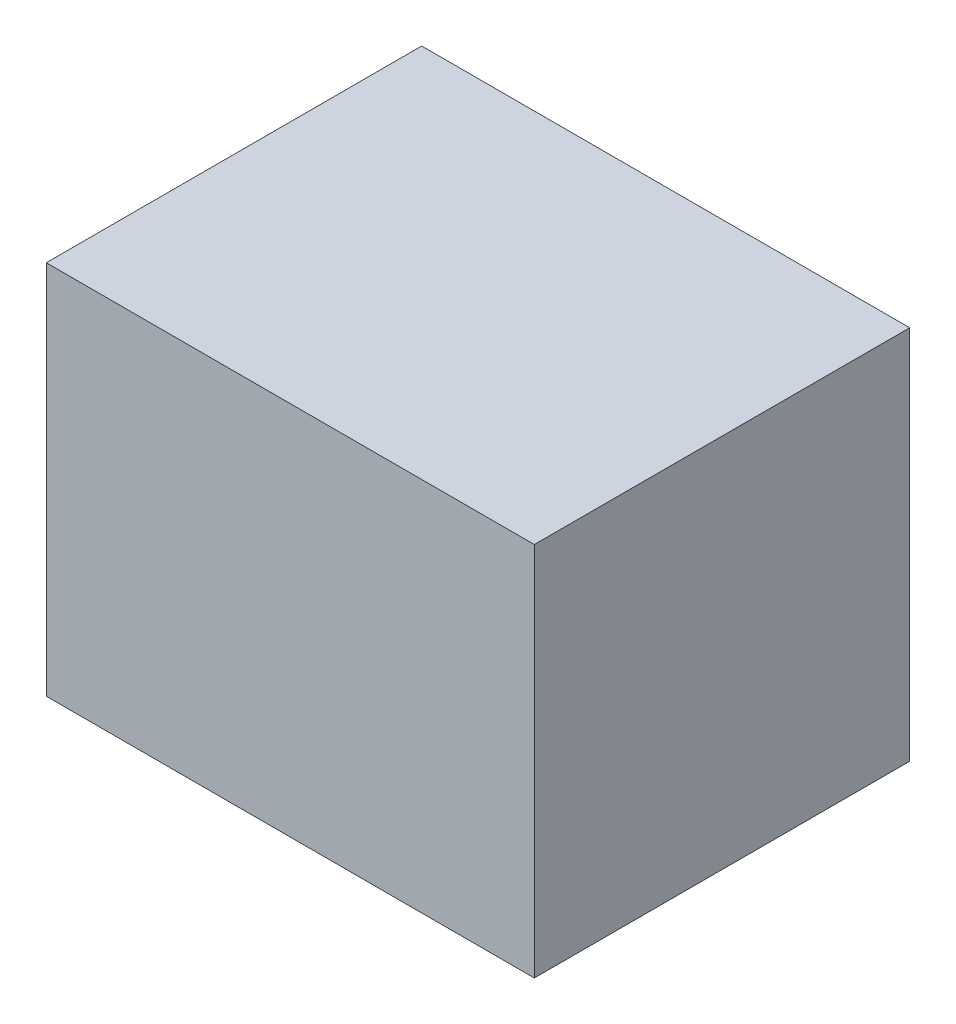
SolidWorks part; units mm, degrees
ref_plane "Front Plane" through (0, 0, 0) normal (0, 0, 1) x (1, 0, 0)
ref_plane "Top Plane" through (0, 0, 0) normal (0, 1, 0) x (1, 0, 0)
ref_plane "Right Plane" through (0, 0, 0) normal (1, 0, 0) x (0, 0, -1)
sketch "Sketch1" plane through (0, 0, 0) normal (0, 1, 0) x (1, 0, 0)
  line L1 (-325, 250) -> (325, 250)
  line L2 (-325, 250) -> (-325, -250)
  line L3 (-325, -250) -> (325, -250)
  line L4 (325, 250) -> (325, -250)
  line L5 (-325, 250) -> (325, -250) construction
  line L6 (-325, -250) -> (325, 250) construction
  point P0 (0, 0)
  dimension "D1" = 500
  dimension "D2" = 650
extrude "Boss-Extrude1" add sketch "Sketch1" along normal blind 500
